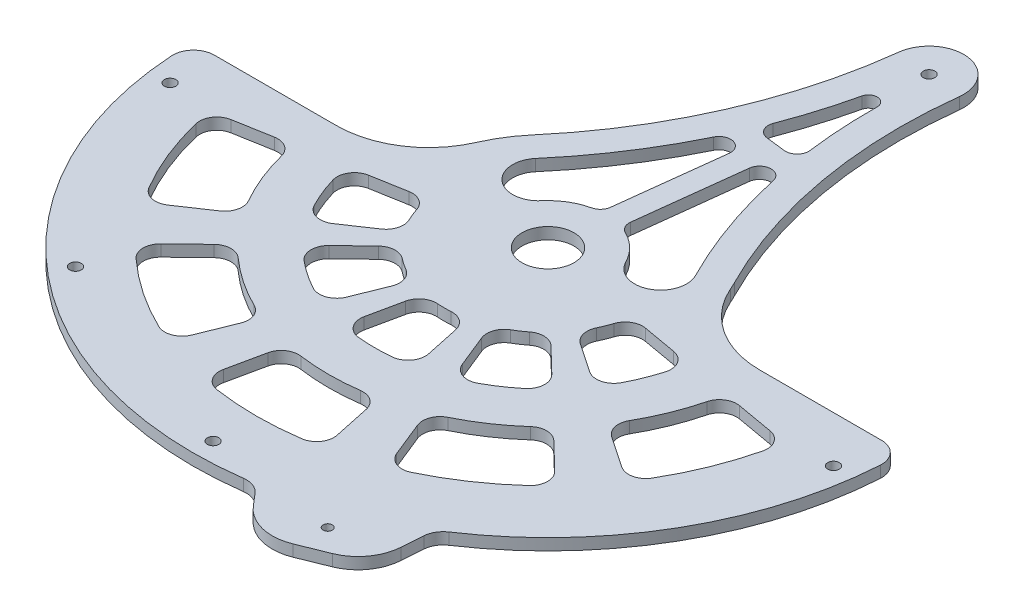
SolidWorks part; units mm, degrees
material "Polycarbonate"
ref_plane "Front Plane" through (0, 0, 0) normal (0, 0, 1) x (1, 0, 0)
ref_plane "Top Plane" through (0, 0, 0) normal (0, 1, 0) x (1, 0, 0)
ref_plane "Right Plane" through (0, 0, 0) normal (1, 0, 0) x (0, 0, -1)
sketch "Sketch1" plane through (0, 0, 0) normal (0, 1, 0) x (1, 0, 0)
  line L0 (76.2, 0) -> (173.0375, 0)
  line L3 (-173.0375, 0) -> (-76.2, 0)
  arc A0 (-169.8625, 0) -> (169.8625, 0) centre (0, 0) ccw construction
  arc A1 (173.0375, 0) -> (-173.0375, 0) centre (0, 0) cw
  arc A2 (-76.2, 0) -> (76.2, 0) centre (0, 0) cw
  dimension "D1" = 169.8625
  dimension "D2" = 3.175
  dimension "D4" = 76.2
extrude "Boss-Extrude1" add sketch "Sketch1" along normal mid plane 6.35
sketch "Sketch2" plane through (0, 3.175, 0) normal (0, 1, 0) x (1, 0, 0)
  line L0 (-76.2, 0) -> (-173.0375, 0) construction
  line L1 (173.0375, 0) -> (76.2, 0) construction
  line L2 (0, 0) -> (0, 34.6103) construction
  line L3 (-78.9658, -53.2631) -> (-47.3795, -31.9579)
  line L4 (-56.2818, -9.924) -> (-93.8029, -16.54)
  line L5 (-60.0635, -148.6623) -> (-45.1963, -111.8647)
  line L6 (-157.9016, -27.8423) -> (-132.9258, -89.6596) construction
  line L7 (-86.7883, -83.8105) -> (-115.3371, -111.3798)
  line L8 (-35.6813, -88.3143) -> (-21.4088, -52.9886)
  line L9 (-41.1103, -39.6997) -> (-68.5171, -66.1662)
  line L10 (-132.9258, -89.6596) -> (-100.0234, -67.4666)
  line L11 (-118.8171, -20.9507) -> (-157.9016, -27.8423)
  line L12 (33.336, -156.8337) -> (25.0845, -118.0135)
  line L13 (-118.8171, -20.9507) -> (-100.0234, -67.4666) construction
  line L14 (-25.0845, -118.0135) -> (-33.336, -156.8337)
  line L15 (19.8036, -93.1686) -> (11.8822, -55.9011)
  line L16 (-11.8822, -55.9011) -> (-19.8036, -93.1686)
  line L17 (115.3371, -111.3798) -> (86.7883, -83.8105)
  line L18 (45.1963, -111.8647) -> (60.0635, -148.6623)
  line L19 (68.5171, -66.1662) -> (41.1103, -39.6997)
  line L20 (21.4088, -52.9886) -> (35.6813, -88.3143)
  line L21 (157.9016, -27.8423) -> (118.8171, -20.9507)
  line L22 (100.0234, -67.4666) -> (132.9258, -89.6596)
  line L23 (93.8029, -16.54) -> (56.2818, -9.924)
  line L24 (47.3795, -31.9579) -> (78.9658, -53.2631)
  line L27 (0, 0) -> (-38.1044, -101.0013) construction
  line L28 (-88.3143, -35.6813) -> (-111.8647, -45.1963) construction
  arc A0 (-157.9016, -27.8423) -> (-132.9258, -89.6596) centre (0, 0) ccw
  arc A1 (-93.8029, -16.54) -> (-78.9658, -53.2631) centre (0, 0) ccw
  arc A2 (-56.2818, -9.924) -> (-47.3795, -31.9579) centre (0, 0) ccw
  arc A3 (-86.7883, -83.8105) -> (-45.1963, -111.8647) centre (0, 0) ccw
  arc A4 (-173.0375, 0) -> (173.0375, 0) centre (0, 0) ccw construction
  arc A5 (-118.8171, -20.9507) -> (-100.0234, -67.4666) centre (0, 0) ccw
  arc A6 (-115.3371, -111.3798) -> (-60.0635, -148.6623) centre (0, 0) ccw
  arc A7 (-68.5171, -66.1662) -> (-35.6813, -88.3143) centre (0, 0) ccw
  arc A8 (-41.1103, -39.6997) -> (-21.4088, -52.9886) centre (0, 0) ccw
  arc A9 (-25.0845, -118.0135) -> (25.0845, -118.0135) centre (0, 0) ccw
  arc A10 (-33.336, -156.8337) -> (33.336, -156.8337) centre (0, 0) ccw
  arc A11 (-19.8036, -93.1686) -> (19.8036, -93.1686) centre (0, 0) ccw
  arc A12 (-11.8822, -55.9011) -> (11.8822, -55.9011) centre (0, 0) ccw
  arc A13 (45.1963, -111.8647) -> (86.7883, -83.8105) centre (0, 0) ccw
  arc A14 (60.0635, -148.6623) -> (115.3371, -111.3798) centre (0, 0) ccw
  arc A15 (35.6813, -88.3143) -> (68.5171, -66.1662) centre (0, 0) ccw
  arc A16 (21.4088, -52.9886) -> (41.1103, -39.6997) centre (0, 0) ccw
  arc A17 (100.0234, -67.4666) -> (118.8171, -20.9507) centre (0, 0) ccw
  arc A18 (132.9258, -89.6596) -> (157.9016, -27.8423) centre (0, 0) ccw
  arc A19 (78.9658, -53.2631) -> (93.8029, -16.54) centre (0, 0) ccw
  arc A20 (47.3795, -31.9579) -> (56.2818, -9.924) centre (0, 0) ccw
  circle A22 centre (0, 0) radius 107.95 construction
  circle A23 centre (0, 0) radius 50.8 construction
  circle A24 centre (-38.1044, -101.0013) radius 61.9125 construction
  circle A25 centre (-17.0909, -45.302) radius 2.3812 construction
  point P19 (-113.4428, -113.4706)
  point P51 (0, 0)
  point P54 (0, 0)
  point P65 (-100.0895, -40.4388)
  dimension "D1" = 12.7
  dimension "D2" = 101.6
  dimension "D3" = 10
  dimension "D5" = 25.4
  dimension "D6" = 57.15
  dimension "D4" = 123.825
  dimension "D8" = 4.7625
  dimension "D9" = 10
  dimension "D10" = 10
  dimension "D7" = 5
extrude "Cut-Extrude1" cut sketch "Sketch2" against normal through all
sketch "Sketch4" plane through (0, 0, 0) normal (0, 1, 0) x (1, 0, 0)
  line L0 (173.0375, 0) -> (195.2625, 0)
  line L4 (-195.2625, 0) -> (-173.0375, 0)
  arc A0 (-195.2625, 0) -> (195.2625, 0) centre (0, 0) ccw
  arc A1 (-173.0375, 0) -> (173.0375, 0) centre (0, 0) ccw construction
  arc A2 (-173.0375, 0) -> (173.0375, 0) centre (0, 0) ccw
  dimension "D1" = 22.225
sketch "Sketch5" plane through (0, -3.175, 0) normal (0, 1, 0) x (1, 0, 0)
  line L0 (-76.2, 0) -> (-173.0375, 0) construction
  line L1 (169.8625, 0) -> (173.0375, 0)
  line L6 (-169.8625, 0) -> (-173.0375, 0)
  arc A0 (-169.8625, 0) -> (169.8625, 0) centre (0, 0) ccw
  arc A1 (-173.0375, 0) -> (173.0375, 0) centre (0, 0) ccw construction
  arc A2 (-173.0375, 0) -> (173.0375, 0) centre (0, 0) ccw
  dimension "D1" = 3.175
extrude "Cut-Extrude2" cut sketch "Sketch5" along normal blind 3.175
extrude "Boss-Extrude2" add sketch "Sketch4" against normal mid plane 6.35 contours A0 L0 A2 L4
sketch "Sketch6" plane through (0, 3.175, 0) normal (0, 1, 0) x (1, 0, 0)
  circle A0 centre (0, 0) radius 14.2875
  dimension "D1" = 28.575
extrude "Cut-Extrude3" cut sketch "Sketch6" against normal through all
sketch "Sketch7" plane through (0, 3.175, 0) normal (0, 1, 0) x (1, 0, 0)
  line L0 (32.2069, -192.5881) -> (53.9687, -217.9881)
  line L1 (53.9687, -217.9881) -> (101.0697, -198.958)
  line L2 (101.0697, -198.958) -> (103.4662, -165.5965)
  line L4 (32.2069, -192.5881) -> (103.4662, -165.5965)
  arc A0 (-195.2625, 0) -> (195.2625, 0) centre (0, 0) ccw construction
  arc A2 (-195.2625, 0) -> (195.2625, 0) centre (0, 0) ccw construction
extrude "Boss-Extrude3" add sketch "Sketch7" against normal through all contours L4 L2 L1 L0
sketch "Sketch8" plane through (0, 3.175, 0) normal (0, 1, 0) x (-1, 0, 0)
  line L1 (-67.8365, 179.0923) -> (-77.5192, 208.4731) construction
  line L2 (-53.9687, 217.9881) -> (-101.0697, 198.958) construction
  line L3 (-32.2069, 192.5881) -> (-67.8365, 179.0923) construction
  line L4 (-67.8365, 179.0923) -> (-103.4662, 165.5965) construction
  circle A0 centre (-72.6779, 193.7827) radius 2.54
  point P8 (-72.6779, 193.7827)
  point P14 (-77.5192, 208.4731)
  dimension "D1" = 5.08
extrude "Cut-Extrude4" cut sketch "Sketch8" against normal through all
sketch "Sketch9" plane through (0, 3.175, 0) normal (0, 1, 0) x (1, 0, 0)
  line L0 (-184.15, 0) -> (-173.0375, 0) construction
  line L1 (-195.2625, 0) -> (-76.2, 0) construction
  line L2 (-184.15, 0) -> (-195.2625, 0) construction
  line L3 (182.3899, -25.4) -> (184.15, 0) construction
  line L4 (-184.15, 0) -> (-182.3899, -25.4) construction
  line L5 (182.3899, -25.4) -> (120.9004, -138.904) construction
  line L6 (120.9004, -138.904) -> (0, -184.15) construction
  line L7 (0, -184.15) -> (-120.9004, -138.904) construction
  line L8 (-120.9004, -138.904) -> (-182.3899, -25.4) construction
  circle A0 centre (-182.3899, -25.4) radius 3.175
  circle A1 centre (-120.9004, -138.904) radius 3.175
  circle A2 centre (0, -184.15) radius 3.175
  circle A3 centre (120.9004, -138.904) radius 3.175 construction
  circle A4 centre (182.3899, -25.4) radius 3.175
  circle A5 centre (0, 0) radius 184.15 construction
  circle A6 centre (0, 0) radius 173.0375 construction
  dimension "D1" = 6.35
  dimension "D2" = 25.4
extrude "Cut-Extrude5" cut sketch "Sketch9" against normal through all
fillet "Fillet1" radius 25.4 2 edges at (101.0697, 0, 198.958) (53.9687, 0, 217.9881)
fillet "Fillet2" radius 9.525 40 edges at (-93.8029, 0, 16.54) (-78.9658, 0, 53.2631) (-47.3795, 0, 31.9579) (-56.2818, 0, 9.924) (-118.8171, 0, 20.9507) (157.9016, 0, 27.8423) (132.9258, 0, 89.6596) (118.8171, 0, 20.9507) (100.0234, 0, 67.4666) (47.3795, 0, 31.9579) (78.9658, 0, 53.2631) (93.8029, 0, 16.54) (56.2818, 0, 9.924) (86.7883, 0, 83.8105) (115.3371, 0, 111.3798) (60.0635, 0, 148.6623) (45.1963, 0, 111.8647) (68.5171, 0, 66.1662) (21.4088, 0, 52.9886) (35.6813, 0, 88.3143) (41.1103, 0, 39.6997) (-19.8036, 0, 93.1686) (19.8036, 0, 93.1686) (11.8822, 0, 55.9011) (-11.8822, 0, 55.9011) (25.0845, 0, 118.0135) (33.336, 0, 156.8337) (-33.336, 0, 156.8337) (-25.0845, 0, 118.0135) (-21.4088, 0, 52.9886) (-35.6813, 0, 88.3143) (-68.5171, 0, 66.1662) (-41.1103, 0, 39.6997) (-115.3371, 0, 111.3798) (-60.0635, 0, 148.6623) (-86.7883, 0, 83.8105) (-157.9016, 0, 27.8423) (-132.9258, 0, 89.6596) (-45.1963, 0, 111.8647) (-100.0234, 0, 67.4666)
fillet "Fillet4" radius 11.43 4 edges at (32.2069, 0, 192.5881) (103.4662, 0, 165.5965) (195.2625, 0, 0) (-195.2625, 0, 0)
fillet "Fillet3" radius 50.8 2 edges at (76.2, 0, 0) (-76.2, 0, 0)
sketch "Sketch10" plane through (0, 3.175, 0) normal (0, 1, 0) x (1, 0, 0)
  line L0 (41.1423, 185.0806) -> (3.3077, 189.5694) construction
  arc A0 (67.9289, 34.5268) -> (-57.964, 49.4632) centre (0, 0) ccw
  arc A1 (3.3077, 189.5694) -> (41.1423, 185.0806) centre (22.225, 187.325) cw
  arc A2 (41.1423, 185.0806) -> (67.9289, 34.5268) centre (303.0074, 154.0119) ccw
  arc A3 (69.8385, 30.48) -> (-69.8385, 30.48) centre (0, 0) ccw construction
  arc A4 (3.3077, 189.5694) -> (-57.964, 49.4632) centre (-258.5574, 220.6382) cw
  circle A5 centre (22.225, 187.325) radius 3.175
  point P1 (22.9315, 187.3003)
  point P6 (-57.964, 49.4632)
  point P7 (0, 187.325)
  point P9 (-258.5574, 220.6382)
  dimension "D1" = 19.05
  dimension "D3" = 6.35
  dimension "D2" = 38.1
  dimension "D4" = 187.325
  dimension "D5" = 22.225
extrude "Boss-Extrude4" add sketch "Sketch10" against normal through all contours A2 L0 A5 A4 A0 | L0 A1 A5
sketch "Sketch11" [suppressed] plane through (0, 3.175, 0) normal (0, 1, 0) x (1, 0, 0)
  line L0 (-179.3875, 0) -> (-195.2892, 0)
  line L1 (-87.9882, 0) -> (-192.0613, 0) construction
  line L2 (-195.2892, 0) -> (-195.2358, -3.2275)
  line L3 (179.3875, 0) -> (195.2892, 0)
  line L4 (192.0613, 0) -> (87.9882, 0) construction
  line L5 (195.2892, 0) -> (195.2358, -3.2275)
  line L7 (33.3672, -193.9423) -> (22.1072, -180.8)
  line L8 (33.3672, -193.9423) -> (42.0912, -204.1249) construction
  line L9 (103.3511, -167.1982) -> (104.6985, -148.4419)
  line L10 (102.2045, -183.1606) -> (103.3511, -167.1982) construction
  arc A0 (-195.2358, -3.2275) -> (30.4608, -192.8719) centre (0, 0) ccw construction
  arc A1 (-195.2358, -3.2275) -> (30.4608, -192.8719) centre (0, 0) ccw
  arc A2 (104.8137, -164.7469) -> (195.2358, -3.2275) centre (0, 0) ccw construction
  arc A3 (104.8137, -164.7469) -> (195.2358, -3.2275) centre (0, 0) ccw
  arc A4 (-179.3875, 0) -> (16.6941, -178.609) centre (0, 0) ccw
  arc A5 (179.3875, 0) -> (107.2362, -143.8064) centre (0, 0) cw
  arc A6 (33.3672, -193.9423) -> (30.4608, -192.8719) centre (30.9561, -196.0081) ccw construction
  arc A7 (33.3672, -193.9423) -> (30.4608, -192.8719) centre (30.9561, -196.0081) ccw
  arc A8 (104.8137, -164.7469) -> (103.3511, -167.1982) centre (106.518, -167.4257) ccw construction
  arc A9 (104.8137, -164.7469) -> (103.3511, -167.1982) centre (106.518, -167.4257) ccw
  arc A10 (107.2362, -143.8064) -> (104.6985, -148.4419) centre (111.0322, -148.8969) ccw
  arc A11 (16.6941, -178.609) -> (22.1072, -180.8) centre (17.2851, -184.9315) cw
  dimension "D1" = 15.875
  dimension "D2" = 6.35
extrude "Cut-Extrude7" [suppressed] cut sketch "Sketch11" against normal through all
sketch "Sketch12" plane through (0, 3.175, 0) normal (0, 1, 0) x (1, 0, 0)
  line L0 (0, 0) -> (6.4672, 54.5092) construction
  line L1 (-2.0736, 36.419) -> (4.8505, 94.7799)
  line L2 (10.5379, 34.9227) -> (17.4621, 93.2836)
  line L3 (-35.0199, 29.884) -> (41.0404, 20.8599) construction
  line L4 (7.8852, 112.5328) -> (18.6657, 111.2538)
  line L5 (8.6334, 118.8386) -> (-1.4552, 95.5281) construction
  arc A0 (17.4621, 93.2836) -> (29.9693, 93.9008) centre (23.7679, 92.5355) cw
  arc A1 (14.0463, 158.5868) -> (2.6995, 121.0994) centre (-258.5574, 220.6382) cw
  arc A2 (23.4521, 157.4709) -> (25.712, 118.3691) centre (303.0074, 154.0119) ccw
  arc A3 (14.0463, 158.5868) -> (23.4521, 157.4709) centre (18.69, 157.5298) cw
  arc A4 (2.6995, 121.0994) -> (7.8852, 112.5328) centre (8.6334, 118.8386) ccw
  arc A5 (18.6657, 111.2538) -> (25.712, 118.3691) centre (19.4139, 117.5595) ccw
  arc A10 (-45.8882, 39.1584) -> (-55.2888, 24.13) centre (0, 0) ccw
  arc A11 (-45.8882, 39.1584) -> (19.0721, 187.6991) centre (-258.5574, 220.6382) ccw
  arc A12 (-24.1517, 20.6097) -> (-6.9828, 30.9726) centre (0, 0) cw
  arc A13 (-45.8882, 39.1584) -> (-7.1651, 98.3066) centre (-258.5574, 220.6382) ccw
  circle A14 centre (0, 0) radius 31.75 construction
  arc A15 (-45.8882, 39.1584) -> (-24.1517, 20.6097) centre (-35.0199, 29.884) ccw
  arc A16 (55.2888, 24.13) -> (53.7771, 27.3337) centre (0, 0) ccw
  arc A17 (25.3779, 186.9509) -> (53.7771, 27.3337) centre (303.0074, 154.0119) ccw
  arc A18 (-6.9828, 30.9726) -> (-2.0736, 36.419) centre (-8.3794, 37.1671) ccw
  arc A19 (29.9693, 93.9008) -> (53.7771, 27.3337) centre (303.0074, 154.0119) ccw
  arc A20 (53.7771, 27.3337) -> (28.3037, 14.3862) centre (41.0404, 20.8599) cw
  arc A21 (28.3037, 14.3862) -> (14.0364, 28.4788) centre (0, 0) ccw
  arc A22 (14.0364, 28.4788) -> (10.5379, 34.9227) centre (16.8437, 34.1746) cw
  arc A23 (4.8505, 94.7799) -> (-7.1651, 98.3066) centre (-1.4552, 95.5281) ccw
  point P27 (3.0102, 25.372)
  point P42 (6.1112, 113.011)
  point P43 (1.0669, 101.3557)
  dimension "D3" = 63.5
  dimension "D4" = 12.7
  dimension "D5" = 6.35
  dimension "D6" = 6.35
  dimension "D7" = 4.7625
  dimension "D8" = 6.35
  dimension "D9" = 12.7
  dimension "D1" = 15.875
  dimension "D2" = 15.875
extrude "Cut-Extrude8" cut sketch "Sketch12" against normal through all
